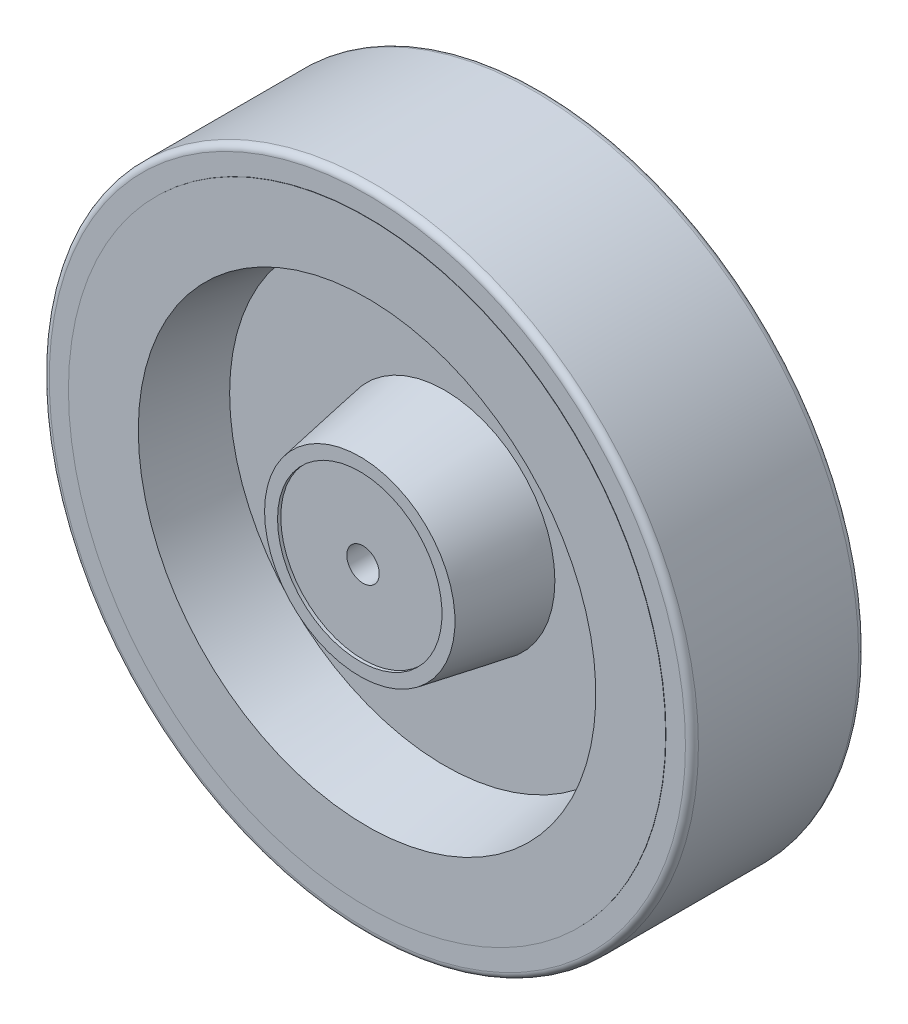
SolidWorks part; units mm, degrees
ref_plane "Front Plane" through (0, 0, 0) normal (0, 0, 1) x (1, 0, 0)
ref_plane "Top Plane" through (0, 0, 0) normal (0, 1, 0) x (1, 0, 0)
ref_plane "Right Plane" through (0, 0, 0) normal (1, 0, 0) x (0, 0, -1)
sketch "Sketch1" plane through (0, 0, 0) normal (0, 0, 1) x (1, 0, 0)
  circle A0 centre (0, 0) radius 150
  circle A1 centre (0, 0) radius 138
  dimension "D1" = 300
  dimension "D2" = 12
extrude "Boss-Extrude1" add sketch "Sketch1" along normal mid plane 80
fillet "Fillet4" radius 3 2 edges at (150, 0, -40) (150, 0, 40)
sketch "Sketch3" plane through (0, 0, 0) normal (0, 1, 0) x (1, 0, 0)
  line L0 (0, 71.2413) -> (0, -84.634) construction
  line L1 (0, -42) -> (0, 42)
  line L2 (0, 42) -> (-38, 42)
  line L3 (-38, 42) -> (-38, 43.5)
  line L4 (-38, 43.5) -> (-44, 43.5)
  line L5 (-44, 43.5) -> (-50.9208, 4.25)
  line L6 (-50.9208, 4.25) -> (-99.391, 4.25)
  line L7 (-99.391, 4.25) -> (-105.7185, 40.1351)
  line L8 (-105.7185, 40.1351) -> (-138, 40.1351)
  line L9 (-138, 40.1351) -> (-138, 0.1351)
  line L10 (0, 0) -> (-234.9563, 0) construction
  line L11 (-138, -40.1351) -> (-138, -0.1351)
  line L12 (-105.7185, -40.1351) -> (-138, -40.1351)
  line L13 (-99.391, -4.25) -> (-105.7185, -40.1351)
  line L14 (-50.9208, -4.25) -> (-99.391, -4.25)
  line L15 (-44, -43.5) -> (-50.9208, -4.25)
  line L16 (-38, -43.5) -> (-44, -43.5)
  line L17 (-38, -42) -> (-38, -43.5)
  line L18 (0, -42) -> (-38, -42)
  line L19 (-138, -0.1351) -> (-138, 0)
  line L21 (-138, 0.1351) -> (-138, 0)
  dimension "D1" = 42
  dimension "D2" = 38
  dimension "D3" = 1.5
  dimension "D4" = 6
  dimension "D5" = 100
  dimension "D6" = 100
  dimension "D7" = 40
  dimension "D8" = 8.5
  dimension "D9" = 138
revolve "Revolve6" add sketch "Sketch3" angle 360 about L0
sketch "Sketch4" plane through (0, 0, 0) normal (0, 1, 0) x (1, 0, 0)
  line L0 (-44.3943, 24.25) -> (-44.3943, 4.25)
  line L1 (50.9208, 4.25) -> (-50.9208, 4.25) construction
  line L2 (-44.3943, 4.25) -> (-79.3943, 4.25)
  line L3 (99.391, 4.25) -> (-99.391, 4.25) construction
  line L4 (-79.3943, 4.25) -> (-79.3943, 7.25)
  line L5 (-79.3943, 7.25) -> (-47.3943, 24.25)
  line L6 (-44, 43.5) -> (-50.9208, 4.25) construction
  line L7 (-47.3943, 24.25) -> (-44.3943, 24.25)
  dimension "D1" = 20
  dimension "D2" = 35
  dimension "D3" = 3
  dimension "D4" = 3
extrude "Boss-Extrude2" add sketch "Sketch4" along normal mid plane 25
sketch "Sketch5" plane through (-20.479, 0, -38.5487) normal (-0.4692, 0, -0.8831) x (-0.8831, 0, 0.4692)
  line L1 (56.7047, -4.57) -> (56.6077, 4.7379)
  line L2 (56.6077, 4.7379) -> (48.4984, 9.3079)
  line L3 (48.4984, 9.3079) -> (40.4859, 4.57)
  line L4 (40.4859, 4.57) -> (40.5829, -4.7379)
  line L5 (40.5829, -4.7379) -> (48.6922, -9.3079)
  line L6 (48.6922, -9.3079) -> (56.7047, -4.57)
  circle A0 centre (48.5953, 0) radius 8.0613 construction
extrude "Boss-Extrude3" add sketch "Sketch5" along normal blind 5.5
sketch "Sketch6" plane through (-23.0594, 0, -43.4059) normal (-0.4692, 0, -0.8831) x (-0.8831, 0, 0.4692)
  line L0 (44.4922, 6.939) -> (55.4536, -11.5983) construction
  line L1 (48.4984, 9.3079) -> (40.4859, 4.57) construction
  circle A0 centre (48.5953, 0) radius 8.0613
extrude "Boss-Extrude4" add sketch "Sketch6" along normal blind 3 draft 30
sketch "Sketch7" plane through (0, 0, 0) normal (0, 1, 0) x (1, 0, 0)
  line L0 (-67.3821, 23.2565) -> (-74.1329, 32.5476)
  line L1 (-61.7926, 26.2259) -> (-72.9716, 20.2871) construction
  line L2 (-61.7926, 26.2259) -> (-67.3821, 23.2565)
  line L3 (-67.3821, 23.2565) -> (-82.0161, 43.3972) construction
  arc A0 (-74.1329, 32.5476) -> (-61.7926, 26.2259) centre (-69.5645, 26.2601) cw
revolve "Revolve7" add sketch "Sketch7" angle 360 about L0
sketch "Sketch8" plane through (0, 0, -42) normal (0, 0, -1) x (-1, 0, 0)
  circle A0 centre (0, 0) radius 7.5
  dimension "D1" = 15
extrude "Cut-Extrude1" cut sketch "Sketch8" against normal through all
equation "\"5.5.00mm\"=25"
